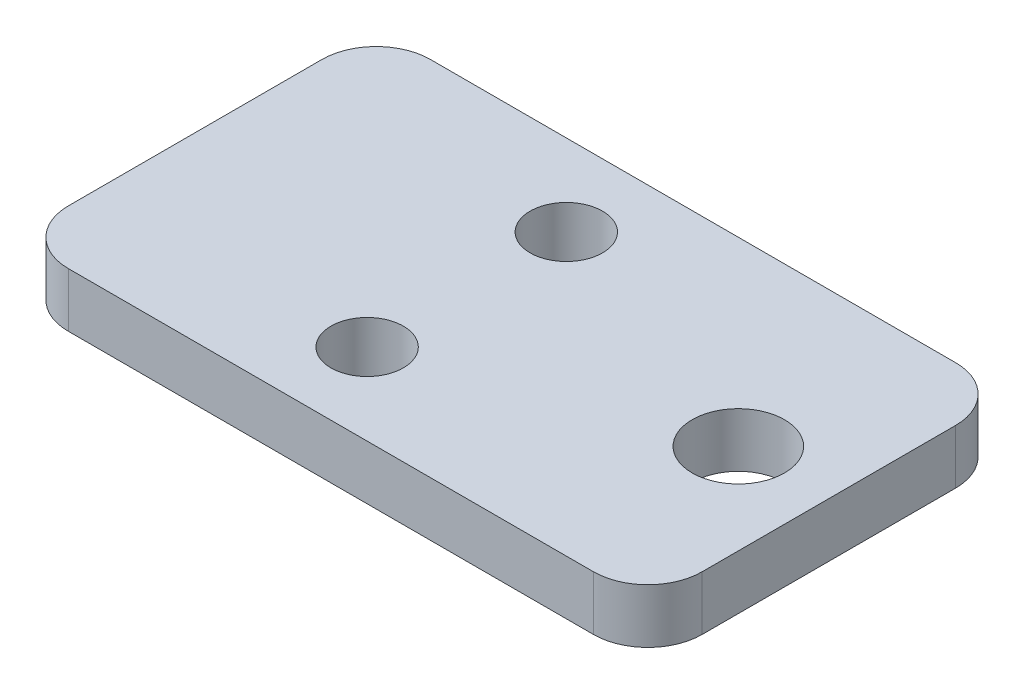
SolidWorks part; units mm, degrees
ref_plane "Front Plane" through (0, 0, 0) normal (0, 0, 1) x (1, 0, 0)
ref_plane "Top Plane" through (0, 0, 0) normal (0, 1, 0) x (1, 0, 0)
ref_plane "Right Plane" through (0, 0, 0) normal (1, 0, 0) x (0, 0, -1)
sketch "Sketch1" plane through (0, 0, 0) normal (0, 1, 0) x (1, 0, 0)
  line L1 (-14.5, 10) -> (14.5, 10)
  line L2 (-17.5, 7) -> (-17.5, -7)
  line L3 (-14.5, -10) -> (14.5, -10)
  line L4 (17.5, 7) -> (17.5, -7)
  line L5 (-17.5, 10) -> (17.5, -10) construction
  line L6 (-17.5, -10) -> (17.5, 10) construction
  arc A0 (17.5, 7) -> (14.5, 10) centre (14.5, 7) ccw
  arc A1 (-17.5, 7) -> (-14.5, 10) centre (-14.5, 7) cw
  arc A2 (-17.5, -7) -> (-14.5, -10) centre (-14.5, -7) ccw
  arc A3 (17.5, -7) -> (14.5, -10) centre (14.5, -7) cw
  circle A4 centre (12.5, 0) radius 2.55
  circle A5 centre (-2.5, 5.5) radius 2
  circle A6 centre (-2.5, -5.5) radius 2
  point P0 (0, 0)
  dimension "D2" = 3
  dimension "D3" = 2
  dimension "D4" = 4.5
  dimension "D5" = 35
  dimension "D6" = 5
  dimension "D7" = 20
  dimension "D1" = 20
extrude "Boss-Extrude1" add sketch "Sketch1" along normal blind 3
